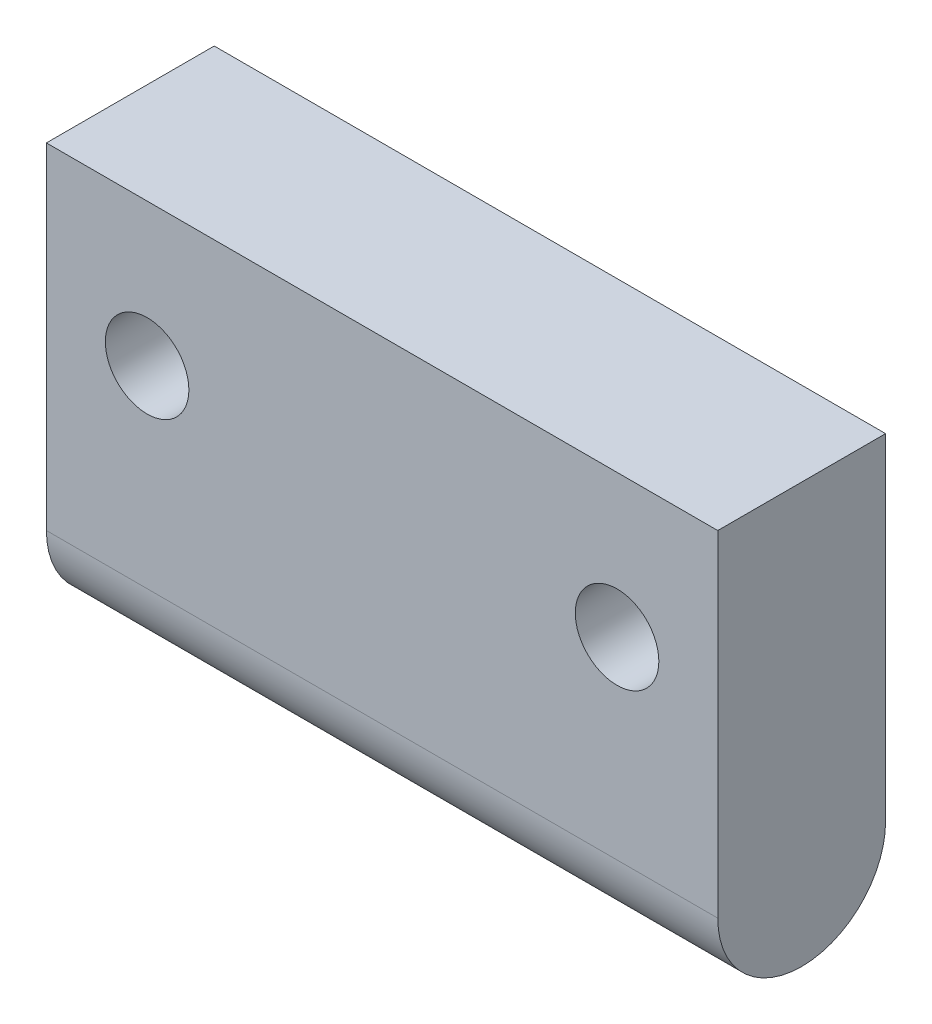
SolidWorks part; units mm, degrees
material "6061-T6 (SS)"
ref_plane "Front Plane" through (0, 0, 0) normal (0, 0, 1) x (1, 0, 0)
ref_plane "Top Plane" through (0, 0, 0) normal (0, 1, 0) x (1, 0, 0)
ref_plane "Right Plane" through (0, 0, 0) normal (1, 0, 0) x (0, 0, -1)
sketch "Sketch2" plane through (0, 0, 0) normal (1, 0, 0) x (0, 0, -1)
  line L0 (0, 20) -> (0, 0)
  line L1 (0, 20) -> (10, 20)
  line L2 (10, 20) -> (10, 0)
  line L3 (0, 0) -> (-8.731, 0) construction
  arc A0 (0, 0) -> (10, 0) centre (5, 0) ccw
  dimension "D1" = 10
  dimension "D2" = 20
extrude "Boss-Extrude1" add sketch "Sketch2" along normal mid plane 40
hole_wizard "#10 Clearance Hole1" positions "Sketch4" profile "Sketch3" hole size "#10" standard "ANSI Inch"
sketch "Sketch4" plane through (0, 0, 0) normal (0, 0, 1) x (1, 0, 0)
  line L0 (-20, 11.5) -> (-17.7043, 11.5) construction
  line L2 (0, 0) -> (0, 4.2721) construction
  line L3 (20, 20) -> (-20, 20) construction
  point P0 (-14, 11.5)
  point P12 (14, 11.5)
  dimension "D1" = 14
  dimension "D2" = 8.5
sketch "Sketch3" plane through (-14, 11.5, 0) normal (1, 0, 0) x (0, -1, 0)
  line L0 (0, 0) -> (0, 31.3257)
  line L1 (0, 31.3257) -> (2.4892, 29.83)
  line L2 (2.4892, 29.83) -> (2.4892, 0)
  line L5 (2.4892, 0) -> (0, 0)
  line L10 (0, 31.3257) -> (-2.4892, 29.83) construction
  line L11 (0, -6.35) -> (0, 107.95) construction
  dimension "Hole Dia." = 4.9784
  dimension "Hole Depth" = 29.83
  dimension "Drill Angle" = 118
